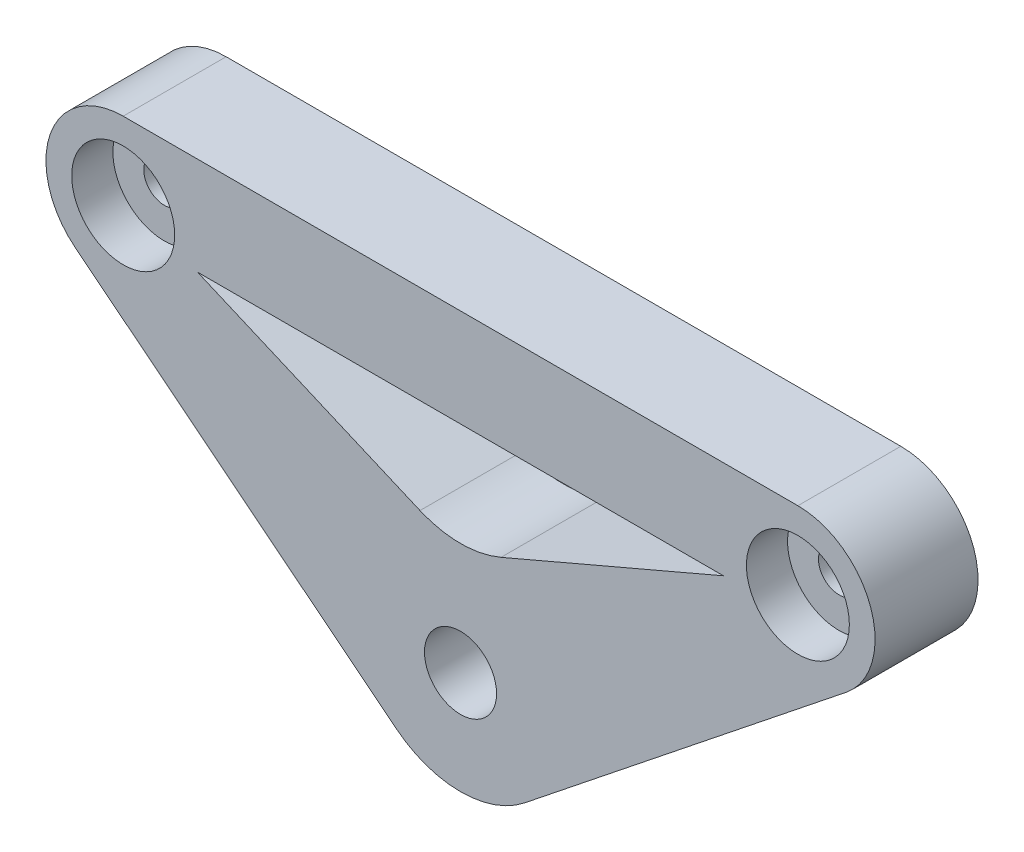
SolidWorks part; units mm, degrees
ref_plane "Front Plane" through (0, 0, 0) normal (0, 0, 1) x (1, 0, 0)
ref_plane "Top Plane" through (0, 0, 0) normal (0, 1, 0) x (1, 0, 0)
ref_plane "Right Plane" through (0, 0, 0) normal (1, 0, 0) x (0, 0, -1)
sketch "Sketch1" plane through (0, 0, 0) normal (0, 0, 1) x (1, 0, 0)
  line L0 (0, 0) -> (-32.7661, 22.9431) construction
  line L1 (-32.7661, 22.9431) -> (32.7661, 22.9431) construction
  line L2 (32.7661, 22.9431) -> (0, 0) construction
  line L3 (-6.2365, -7.817) -> (-37.4435, 17.0803)
  line L4 (6.2365, -7.817) -> (37.4435, 17.0803)
  line L5 (-32.7661, 30.4431) -> (32.7661, 30.4431)
  line L6 (4.5806, 8.8892) -> (-28.8524, 29.3409)
  line L7 (-30.7344, 15.7235) -> (32.7661, 15.4431)
  line L8 (-5.2126, 8.534) -> (28.8566, 29.3436)
  line L9 (-6.416, 15.6161) -> (-25.5402, 20.9338) construction
  line L10 (-25.5402, 20.9338) -> (0, 10) construction
  line L11 (0, 10) -> (25.5402, 20.9338) construction
  line L12 (25.5402, 20.9338) -> (-25.5402, 20.9338) construction
  line L13 (-25.5402, 20.9338) -> (0, 10)
  line L14 (0, 10) -> (25.5402, 20.9338)
  line L15 (25.5402, 20.9338) -> (-25.5402, 20.9338)
  circle A0 centre (-32.7661, 22.9431) radius 2
  circle A1 centre (32.7661, 22.9431) radius 2
  circle A2 centre (0, 0) radius 3.5
  circle A3 centre (-32.7661, 22.9431) radius 7.5
  circle A4 centre (32.7661, 22.9431) radius 7.5
  circle A5 centre (0, 0) radius 10
  dimension "D4" = 7
  dimension "D5" = 4
  dimension "D6" = 4
  dimension "D7" = 15
  dimension "D8" = 15
  dimension "D9" = 20
  dimension "D1" = 40
  dimension "D2" = 40
  dimension "D3" = 110
extrude "Boss-Extrude1" add sketch "Sketch1" along normal blind 10 contours A5 L4 A4 L7 L8 L6 | A4 L8 L7 | A4 L7 A1 | A5 A2 | A5 L8 L6 L7 A3 L3 | A3 L7 L6 | A3 A0 | A4 L5 A3 L6 L7 L8 | A3 L7 L13 | A5 L6 L14 | A5 L13 L8 | A4 L14 L7
fillet "Fillet1" radius 10 1 edges at (0, 10, 5)
sketch "Sketch2" plane through (0, 0, 0) normal (0, 0, -1) x (-1, 0, 0)
  circle A0 centre (0, 0) radius 6.5
  dimension "D1" = 13
extrude "Cut-Extrude1" cut sketch "Sketch2" against normal blind 5
sketch "Sketch3" plane through (0, 0, 10) normal (0, 0, 1) x (1, 0, 0)
  circle A0 centre (-32.7661, 22.9431) radius 5
  circle A1 centre (32.7661, 22.9431) radius 5
  dimension "D1" = 10
  dimension "D2" = 10
extrude "Cut-Extrude2" cut sketch "Sketch3" against normal blind 4
